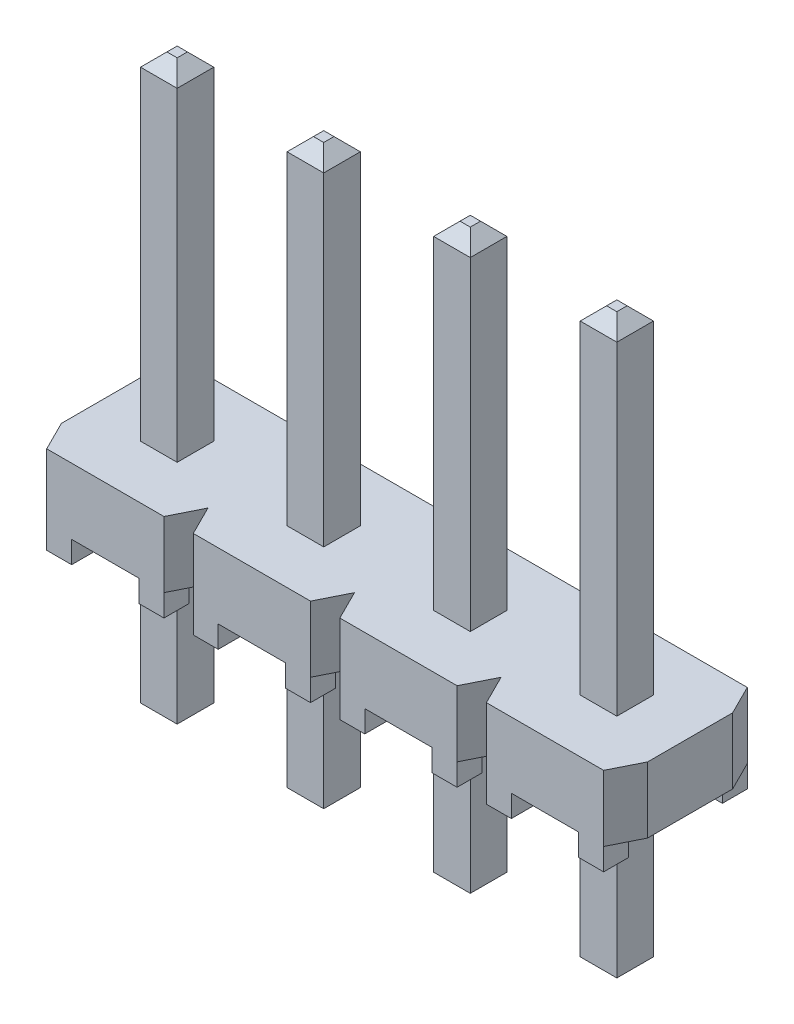
SolidWorks part; units mm, degrees
material "普通碳钢"
ref_plane "Front" through (0, 0, 0) normal (0, 0, 1) x (1, 0, 0)
ref_plane "Top" through (0, 0, 0) normal (0, 1, 0) x (1, 0, 0)
ref_plane "Side" through (0, 0, 0) normal (1, 0, 0) x (0, 0, -1)
sketch "Sketch1" plane through (0, 0, 0) normal (0, 1, 0) x (1, 0, 0)
  line L0 (5.08, -1.2446) -> (-5.08, 1.2446) construction
  line L1 (-5.08, 1.2446) -> (5.08, 1.2446)
  line L2 (-5.08, 1.2446) -> (-5.08, -1.2446)
  line L3 (-5.08, -1.2446) -> (5.08, -1.2446)
  line L4 (5.08, 1.2446) -> (5.08, -1.2446)
  dimension "D1" = 10.16
  dimension "D2" = 2.4892
extrude "Base-Extrude" add sketch "Sketch1" along normal mid plane 1.143
sketch "Sketch3" plane through (0, 0.5715, 0) normal (0, 1, 0) x (-1, 0, 0)
  line L0 (7.5339, 0) -> (10.4044, 0) construction
  line L1 (2.286, 1.2446) -> (2.794, 1.2446)
  line L2 (2.286, -1.2446) -> (2.794, -1.2446)
  line L3 (2.794, 1.2446) -> (2.54, 0.7366)
  line L4 (2.794, -1.2446) -> (2.54, -0.7366)
  line L5 (2.54, 0.7366) -> (2.286, 1.2446)
  line L6 (2.54, -0.7366) -> (2.286, -1.2446)
  line L7 (2.54, 1.2446) -> (2.54, 0.7366) construction
  line L8 (2.54, -1.2446) -> (2.54, -0.7366) construction
  line L9 (5.08, 1.2446) -> (-5.08, 1.2446) construction
  line L11 (3.81, -1.4521) -> (3.81, 2.3817) construction
  line L12 (5.08, -0.7366) -> (5.334, -1.2446)
  line L13 (5.08, 0.7366) -> (5.334, 1.2446)
  line L14 (4.826, -1.2446) -> (5.08, -0.7366)
  line L15 (4.826, 1.2446) -> (5.08, 0.7366)
  line L16 (5.334, -1.2446) -> (4.826, -1.2446)
  line L17 (5.334, 1.2446) -> (4.826, 1.2446)
  line L18 (5.08, -1.2446) -> (5.08, 1.2446) construction
  dimension "D1" = 0.508
  dimension "D2" = 0.508
  dimension "D3" = 1.27
  dimension "D4" = 1.27
extrude "Snap Grooves" cut sketch "Sketch3" against normal through all
sketch "Sketch4" plane through (0, -0.5715, 0) normal (0, -1, 0) x (1, 0, 0)
  line L0 (-3.81, 1.3819) -> (-3.81, -1.499) construction
  line L1 (-4.826, 1.2446) -> (-2.794, 1.2446) construction
  line L2 (-4.826, 1.2446) -> (-4.3942, 1.2446)
  line L3 (-4.826, 1.2446) -> (-4.826, 0.8128)
  line L4 (-4.826, 0.8128) -> (-4.3942, 0.8128)
  line L5 (-4.3942, 1.2446) -> (-4.3942, 0.8128)
  line L6 (-3.2258, 1.2446) -> (-3.2258, 0.8128)
  line L7 (-2.794, 0.8128) -> (-3.2258, 0.8128)
  line L8 (-2.794, 1.2446) -> (-2.794, 0.8128)
  line L9 (-2.794, 1.2446) -> (-3.2258, 1.2446)
  line L11 (-5.08, -0.7366) -> (-5.08, 0.7366) construction
  line L12 (-9.3213, 0) -> (-10.8923, 0) construction
  line L14 (-2.794, -1.2446) -> (-3.2258, -1.2446)
  line L15 (-2.794, -1.2446) -> (-2.794, -0.8128)
  line L16 (-2.794, -0.8128) -> (-3.2258, -0.8128)
  line L17 (-3.2258, -1.2446) -> (-3.2258, -0.8128)
  line L18 (-4.3942, -1.2446) -> (-4.3942, -0.8128)
  line L19 (-4.826, -0.8128) -> (-4.3942, -0.8128)
  line L20 (-4.826, -1.2446) -> (-4.826, -0.8128)
  line L21 (-4.826, -1.2446) -> (-4.3942, -1.2446)
  dimension "D1" = 0.4318
  dimension "D2" = 0.4318
  dimension "D3" = 1.27
extrude "Standoffs" add sketch "Sketch4" along normal blind 0.381
pattern_linear "Position Pattern" count 4 spacing 2.54 along (1, 0, 0) of "Snap Grooves", "Standoffs"
ref_plane "Position 1 Plane" through (-3.81, 0, 0) normal (-1, 0, 0) x (0, 0, 1)
sketch "Sketch5" plane through (-3.81, 0, 0) normal (-1, 0, 0) x (0, 0, 1)
  line L0 (0, 6.4135) -> (0, -3.5865) construction
  line L1 (-0.3175, 6.4135) -> (0.3175, 6.4135)
  line L2 (-0.3175, 6.4135) -> (-0.3175, -3.5865)
  line L3 (-0.3175, -3.5865) -> (0.3175, -3.5865)
  line L4 (0.3175, 6.4135) -> (0.3175, -3.5865)
  line L5 (1.2446, -0.5715) -> (1.2446, 0.5715) construction
  line L6 (-0.7366, 0.5715) -> (0.7366, 0.5715) construction
  dimension "D1" = 1.2446
  dimension "D2" = 0.635
  dimension "D3" = 5.842
  dimension "D4" = 10
extrude "Terminal -TH" add sketch "Sketch5" along normal mid plane 0.635
chamfer "T1 Tip1" distance 0.2286 angle 45 8 edges at (-3.4925, 6.4135, 0) (-3.81, 6.4135, -0.3175) (-4.1275, 6.4135, 0) (-3.81, 6.4135, 0.3175) (-3.81, -3.5865, -0.3175) (-4.1275, -3.5865, 0) (-3.81, -3.5865, 0.3175) (-3.4925, -3.5865, 0)
pattern_linear "Terminal Pattern" count 1 spacing 2.54 along (0, 0, 1) count 4 spacing 2.54 along (1, 0, 0) of "Terminal -TH", "T1 Tip1"
ref_plane "Initial -S Polarize Plane" through (6.35, 0, 0) normal (1, 0, 0) x (0, 0, -1)
ref_plane "-S Polarize Plane" through (3.81, 0, 0) normal (1, 0, 0) x (0, 0, -1)
ref_plane "Initial -D Polarize Plane" through (-6.35, 0, 0) normal (-1, 0, 0) x (0, 0, 1)
ref_plane "-D Polarize Plane" through (-5.08, 0, 0) normal (-1, 0, 0) x (0, 0, 1)
